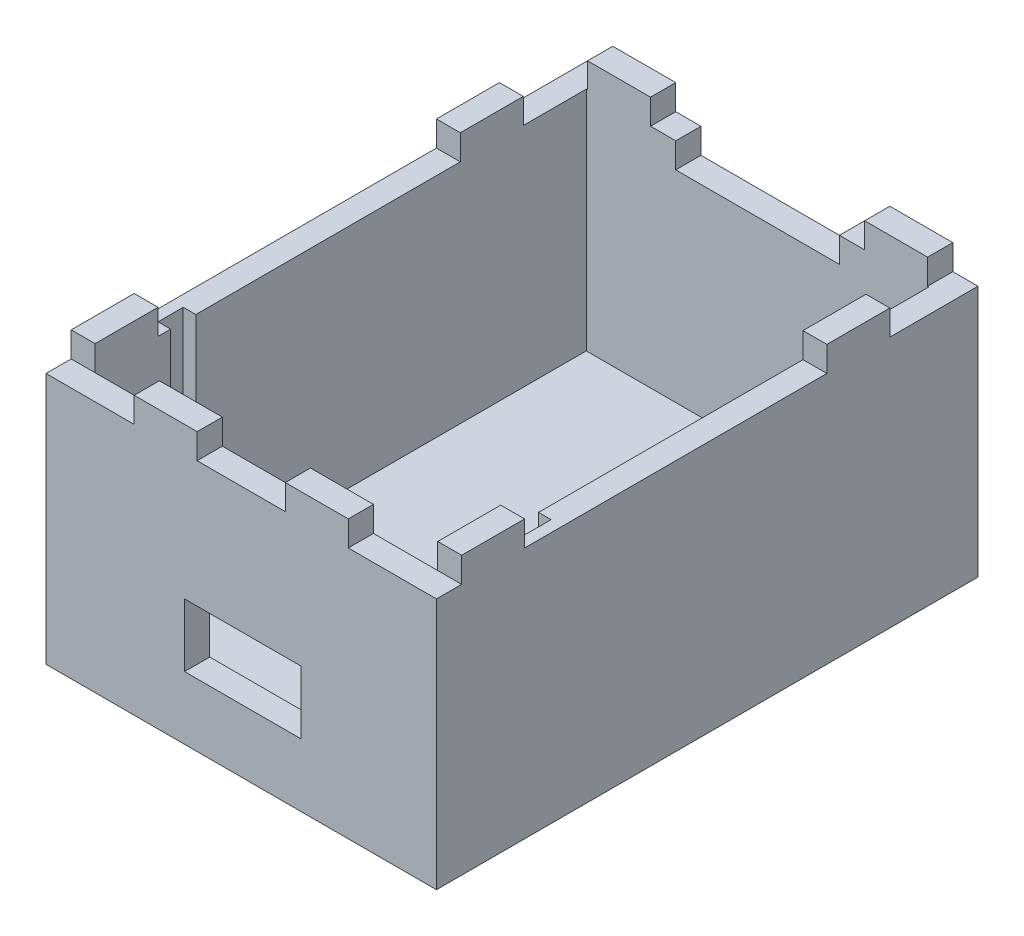
SolidWorks part; units mm, degrees
ref_plane "Front Plane" through (0, 0, 0) normal (0, 0, 1) x (1, 0, 0)
ref_plane "Top Plane" through (0, 0, 0) normal (0, 1, 0) x (1, 0, 0)
ref_plane "Right Plane" through (0, 0, 0) normal (1, 0, 0) x (0, 0, -1)
sketch "Sketch1" plane through (0, 0, 0) normal (0, 1, 0) x (1, 0, 0)
  line L1 (-15.5, 21.5) -> (15.5, 21.5)
  line L2 (-15.5, 21.5) -> (-15.5, -21.5)
  line L3 (-15.5, -21.5) -> (15.5, -21.5)
  line L4 (15.5, 21.5) -> (15.5, -21.5)
  line L5 (-15.5, 21.5) -> (15.5, -21.5) construction
  line L6 (-15.5, -21.5) -> (15.5, 21.5) construction
  point P0 (0, 0)
  dimension "D1" = 43
  dimension "D2" = 31
extrude "Boss-Extrude1" add sketch "Sketch1" along normal blind 22 contours L2 L1 L4 L3
sketch "Sketch2" plane through (0, 22, 0) normal (0, 1, 0) x (1, 0, 0)
  line L0 (-13.604, 21.5) -> (-13.604, 19.5)
  line L1 (-15.5, 21.5) -> (15.5, 21.5) construction
  line L2 (-15.5, -20.406) -> (-13.5, -20.406)
  line L3 (-15.5, 21.5) -> (-15.5, -21.5) construction
  line L5 (13.604, -19.5) -> (-13.604, -19.5)
  line L6 (13.604, -19.5) -> (13.604, 19.5)
  line L7 (13.604, 19.5) -> (-13.604, 19.5)
  line L8 (-13.604, -19.5) -> (-13.604, 19.5)
  line L9 (13.604, -19.5) -> (-13.604, 19.5) construction
  line L10 (13.604, 19.5) -> (-13.604, -19.5) construction
  point P8 (0, 0)
  dimension "D1" = 2
  dimension "D2" = 2
extrude "Cut-Extrude1" cut sketch "Sketch2" against normal blind 20 contours L8 L5 L6 L7
sketch "Sketch3" plane through (0, 0, 21.5) normal (0, 0, 1) x (1, 0, 0)
  line L0 (-15.5, 0) -> (-4.5008, 0)
  line L1 (-15.5, 0) -> (15.5, 0) construction
  line L2 (15.5, 0) -> (4.5, 0)
  line L3 (-15.5, 0) -> (-15.5, 5)
  line L4 (-15.5, 22) -> (-15.5, 0) construction
  line L5 (-15.5, 5) -> (-15.5, 10)
  line L7 (-4.5008, 0) -> (4.7533, 0)
  line L8 (-4.5008, 0) -> (-4.5008, 5)
  line L9 (-4.5008, 5) -> (4.7533, 5)
  line L10 (4.7533, 0) -> (4.7533, 5)
  line L11 (-4.5008, 5) -> (4.7533, 5)
  line L12 (-4.5008, 5) -> (-4.5008, 10)
  line L13 (-4.5008, 10) -> (4.7533, 10)
  line L14 (4.7533, 5) -> (4.7533, 10)
  dimension "D1" = 11
  dimension "D2" = 10.9992
  dimension "D3" = 5
  dimension "D4" = 5
extrude "Cut-Extrude2" cut sketch "Sketch3" against normal blind 20 contours L9 L14 L13 L12
sketch "Sketch4" plane through (0, 0, 21.5) normal (0, 0, 1) x (1, 0, 0)
  line L0 (3.5, 20) -> (8.5, 20)
  line L1 (-15.5, 22) -> (-15.5, 20)
  line L2 (-15.5, 22) -> (-15.5, 0) construction
  line L3 (-15.5, 22) -> (15.5, 22) construction
  line L4 (-15.5, 20) -> (-8.5, 20)
  line L5 (-15.5, 20) -> (-15.5, 22)
  line L6 (-15.5, 22) -> (-8.5, 22)
  line L7 (-8.5, 20) -> (-8.5, 22)
  line L8 (-8.5, 20) -> (-3.5, 20)
  line L9 (-3.5, 20) -> (3.5, 20)
  line L10 (-3.5, 20) -> (-3.5, 22)
  line L11 (-3.5, 22) -> (3.5, 22)
  line L12 (3.5, 20) -> (3.5, 22)
  line L13 (15.5, 22) -> (15.5, 0) construction
  line L14 (8.5, 20) -> (15.5, 20)
  line L15 (8.5, 20) -> (8.5, 22)
  line L16 (8.5, 22) -> (15.5, 22)
  line L17 (15.5, 20) -> (15.5, 22)
  line M21 (15.5, 0) -> (15.5, 22)
  line M22 (15.5, 22) -> (-15.5, 22)
  line M23 (-15.5, 22) -> (-15.5, 0)
  dimension "D1" = 2
  dimension "D2" = 7
  dimension "D3" = 7
extrude "Cut-Extrude3" cut sketch "Sketch4" against normal blind 2 contours L4 L7 M22 M23 | L9 L12 L10 M22 | L15 L14 M21 M22
sketch "Sketch5" plane through (0, 0, -21.5) normal (0, 0, -1) x (-1, 0, 0)
  line L0 (-13.5, 20) -> (-8.5, 20)
  line L1 (-15.5, 22) -> (-13.5, 22)
  line L2 (-15.5, 22) -> (-15.5, 20)
  line L3 (-15.5, 20) -> (-13.5, 20)
  line L4 (-13.5, 22) -> (-13.5, 20)
  line L5 (15.5, 22) -> (-15.5, 22) construction
  line L6 (-8.5, 20) -> (8.5, 20)
  line L7 (-8.5, 20) -> (-8.5, 22)
  line L8 (-8.5, 22) -> (8.5, 22)
  line L9 (8.5, 20) -> (8.5, 22)
  line L10 (8.5, 20) -> (13.5, 20)
  line L11 (-8.5, 19.6434) -> (-6.5003, 19.6434)
  line L12 (13.5, 20) -> (15.5, 20)
  line L13 (13.5, 20) -> (13.5, 22)
  line L14 (13.5, 22) -> (15.5, 22)
  line L15 (15.5, 20) -> (15.5, 22)
  line L16 (8.5067, 19.6434) -> (6.5067, 19.6434)
  line L18 (-6.5003, 20) -> (6.4997, 20)
  line L19 (-6.5003, 20) -> (-6.5003, 18)
  line L20 (-6.5003, 18) -> (6.4997, 18)
  line L21 (6.4997, 20) -> (6.4997, 18)
  dimension "D1" = 2
  dimension "D2" = 2
  dimension "D3" = 5
  dimension "D4" = 17
  dimension "D5" = 5
  dimension "D6" = 2
  dimension "D7" = 2
  dimension "D8" = 13
extrude "Cut-Extrude6" cut sketch "Sketch5" against normal blind 2 contours L6 L9 L7 | L21 L6 L19 L20 | L13 L12 L6 L7 | L4 L7 L9 L3
sketch "Sketch6" plane through (-15.5, 0, 0) normal (-1, 0, 0) x (0, 0, 1)
  line L0 (-19.5, 20) -> (-14.5, 20)
  line L1 (21.5, 20) -> (14.5, 20)
  line L2 (14.5, 20) -> (9.5, 20)
  line L11 (-14.5, 20) -> (-9.5, 20)
  line L14 (-9.5, 20) -> (9.5, 20)
  line L15 (-9.5, 20) -> (-9.5, 22)
  line L16 (-9.5, 22) -> (9.5, 22)
  line L17 (9.5, 20) -> (9.5, 22)
  line L18 (-19.5, 22) -> (19.5, 22) construction
  line L20 (-14.5, 20) -> (-19.5, 20)
  line L21 (-14.5, 20) -> (-14.5, 22)
  line L22 (-14.5, 22) -> (-19.5, 22)
  line L23 (-19.5, 20) -> (-19.5, 22)
  line L24 (9.5, 20) -> (14.5, 20)
  line L25 (9.5, 20) -> (9.5, 22)
  line L26 (9.5, 22) -> (14.5, 22)
  line L27 (14.5, 20) -> (14.5, 22)
  line M8 (-19.5, 22) -> (-19.5, 20)
  line M15 (19.5, 22) -> (-19.5, 22)
  dimension "D1" = 5
  dimension "D2" = 7
  dimension "D3" = 5
  dimension "D4" = 5
extrude "Cut-Extrude10" cut sketch "Sketch6" against normal blind 34 contours L0 L21 M15 M8 | L14 L17 L15 M15 | L2 L27 L17 M15
sketch "Sketch10" plane through (0, 2, 0) normal (0, 1, 0) x (1, 0, 0)
  line L0 (13.604, -14.5) -> (13.604, -13.5)
  line L1 (13.604, -19.5) -> (13.604, 19.5) construction
  line L3 (13.604, -13.5) -> (14.604, -13.5)
  line L4 (13.604, -13.5) -> (13.604, -11.5)
  line L5 (13.604, -11.5) -> (14.604, -11.5)
  line L6 (14.604, -13.5) -> (14.604, -11.5)
  line M6 (13.604, -19.5) -> (13.604, 19.5)
  dimension "D1" = 1
  dimension "D2" = 1
  dimension "D3" = 2
extrude "Cut-Extrude11" cut sketch "Sketch10" along normal blind 18 contours L3 L6 L5 M6
sketch "Sketch11" plane through (0, 20, 0) normal (0, 1, 0) x (1, 0, 0)
  line L0 (-13.604, -14.5) -> (-13.604, -13.5)
  line L1 (-13.604, -19.5) -> (-13.604, 19.5) construction
  line L2 (-13.604, -14.5) -> (-13.604, 9.5) construction
  line L4 (-13.604, -13.5) -> (-14.604, -13.5)
  line L5 (-13.604, -13.5) -> (-13.604, -11.5)
  line L6 (-13.604, -11.5) -> (-14.604, -11.5)
  line L7 (-14.604, -13.5) -> (-14.604, -11.5)
  line M4 (-13.604, -14.5) -> (-13.604, 9.5)
  dimension "D1" = 1
  dimension "D2" = 2
  dimension "D3" = 1
extrude "Cut-Extrude12" cut sketch "Sketch11" against normal blind 15 contours L7 L4 L6 M4
sketch "Sketch12" plane through (0, 2, 0) normal (0, 1, 0) x (1, 0, 0)
  line L1 (14.604, -11.5) -> (13.604, -11.5)
  line L2 (14.604, -11.5) -> (14.604, -13.5)
  line L3 (14.604, -13.5) -> (13.604, -13.5)
  line L4 (13.604, -11.5) -> (13.604, -13.5)
extrude "Boss-Extrude3" add sketch "Sketch12" along normal blind 2
